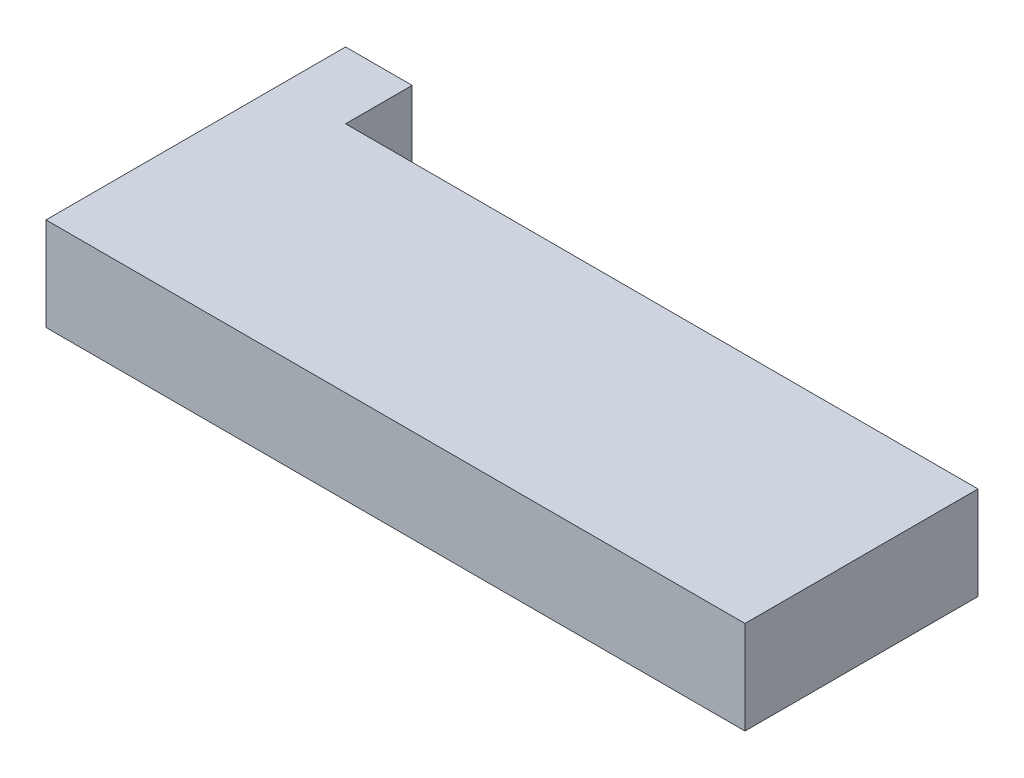
SolidWorks part; units mm, degrees
ref_plane "Front Plane" through (0, 0, 0) normal (0, 0, 1) x (1, 0, 0)
ref_plane "Top Plane" through (0, 0, 0) normal (0, 1, 0) x (1, 0, 0)
ref_plane "Right Plane" through (0, 0, 0) normal (1, 0, 0) x (0, 0, -1)
sketch "Sketch1" plane through (0, 0, 0) normal (0, 1, 0) x (1, 0, 0)
  line L0 (0, 17.5) -> (0, -17.5) construction
  line L1 (-52.5, 17.5) -> (52.5, 17.5)
  line L2 (-52.5, 17.5) -> (-52.5, -17.5)
  line L3 (-52.5, -17.5) -> (52.5, -17.5)
  line L4 (52.5, 17.5) -> (52.5, -17.5)
  point P6 (0, 0)
  dimension "D1" = 105
  dimension "D2" = 35
extrude "Boss-Extrude1" add sketch "Sketch1" along normal blind 14
sketch "Sketch2" plane through (0, 0, -17.5) normal (0, 0, -1) x (-1, 0, 0)
  line L0 (-52.5, 0) -> (52.5, 0) construction
  line L1 (52.5, 14) -> (42.5, 14)
  line L2 (52.5, 14) -> (52.5, 0)
  line L3 (52.5, 0) -> (42.5, 0)
  line L4 (42.5, 14) -> (42.5, 0)
  dimension "D1" = 10
extrude "Boss-Extrude2" add sketch "Sketch2" along normal blind 10
